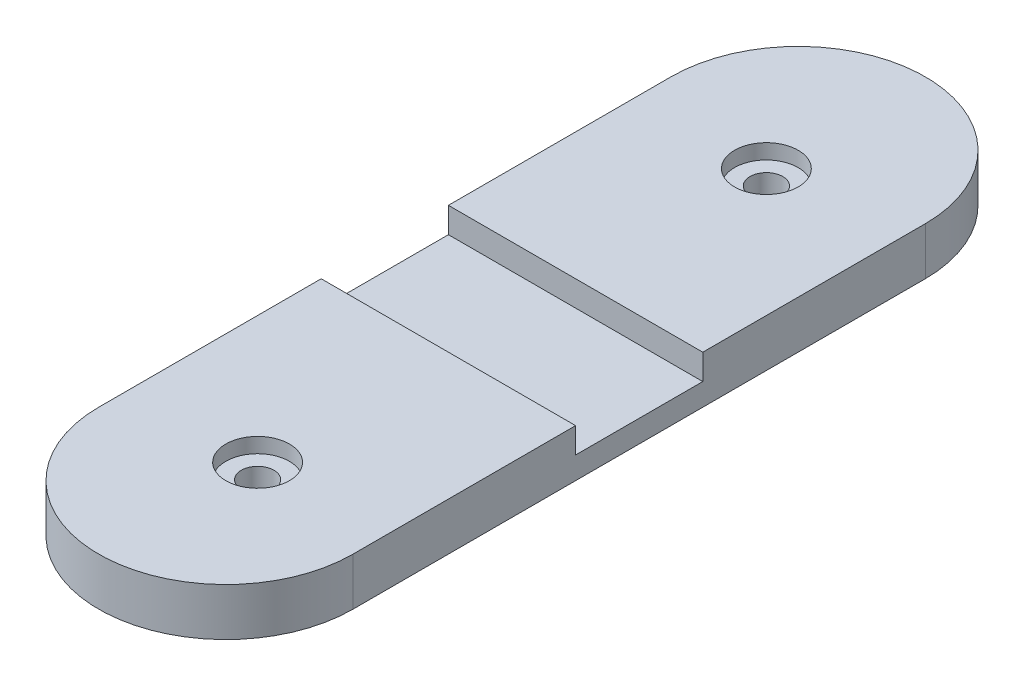
SolidWorks part; units mm, degrees
ref_plane "Front Plane" through (0, 0, 0) normal (0, 0, 1) x (1, 0, 0)
ref_plane "Top Plane" through (0, 0, 0) normal (0, 1, 0) x (1, 0, 0)
ref_plane "Right Plane" through (0, 0, 0) normal (1, 0, 0) x (0, 0, -1)
sketch "Sketch1" plane through (0, 0, 0) normal (0, 1, 0) x (1, 0, 0)
  line L0 (-12.7, -28.575) -> (-12.7, 28.575)
  line L1 (12.7, 28.575) -> (12.7, -28.575)
  line L2 (-12.7, 0) -> (12.7, 0) construction
  line L3 (0, 41.275) -> (0, -41.275) construction
  arc A0 (-12.7, 28.575) -> (12.7, 28.575) centre (0, 28.575) cw
  arc A1 (-12.7, -28.575) -> (12.7, -28.575) centre (0, -28.575) ccw
  dimension "D2" = 12.7
  dimension "D1" = 82.55
extrude "Boss-Extrude1" add sketch "Sketch1" along normal blind 4.7625
hole_wizard "CBORE for #4 Button Head Cap Screw1" positions "Sketch5" profile "Sketch4" counterbore size "#4" standard "Ansi Inch" end condition through all
sketch "Sketch5" plane through (0, 4.7625, 0) normal (0, 1, 0) x (-1, 0, 0)
  line L0 (0, 0) -> (16.1552, 0) construction
  point P0 (0, 25.4)
  point P9 (0, -25.4)
  dimension "D1" = 50.8
sketch "Sketch4" plane through (0, 4.7625, 25.4) normal (1, 0, 0) x (0, 0, 1)
  line L0 (0, 0) -> (0, 4.7625)
  line L1 (0, 4.7625) -> (1.6319, 4.7625)
  line L3 (1.6319, 4.7625) -> (1.632, 1.4986)
  line L4 (1.632, 1.4986) -> (3.175, 1.4986)
  line L5 (3.175, 1.4986) -> (3.175, 0)
  line L7 (3.175, 0) -> (0, 0)
  line L11 (0, -6.35) -> (0, 107.95) construction
  dimension "Thru Hole Dia." = 3.2639
  dimension "Thru Hole Depth" = 4.7625
  dimension "C'Bore Dia." = 6.35
  dimension "C'Bore Depth" = 1.4986
sketch "Sketch6" plane through (0, 4.7625, 0) normal (0, 1, 0) x (1, 0, 0)
  line L0 (-12.7, 28.575) -> (-12.7, -28.575) construction
  line L1 (12.7, 6.35) -> (-12.7, 6.35)
  line L2 (12.7, 6.35) -> (12.7, -6.35)
  line L3 (12.7, -6.35) -> (-12.7, -6.35)
  line L4 (-12.7, 6.35) -> (-12.7, -6.35)
  line L5 (12.7, 6.35) -> (-12.7, -6.35) construction
  line L6 (12.7, -6.35) -> (-12.7, 6.35) construction
  point P0 (0, 0)
  dimension "D1" = 12.7
extrude "Cut-Extrude1" cut sketch "Sketch6" against normal blind 2.54
